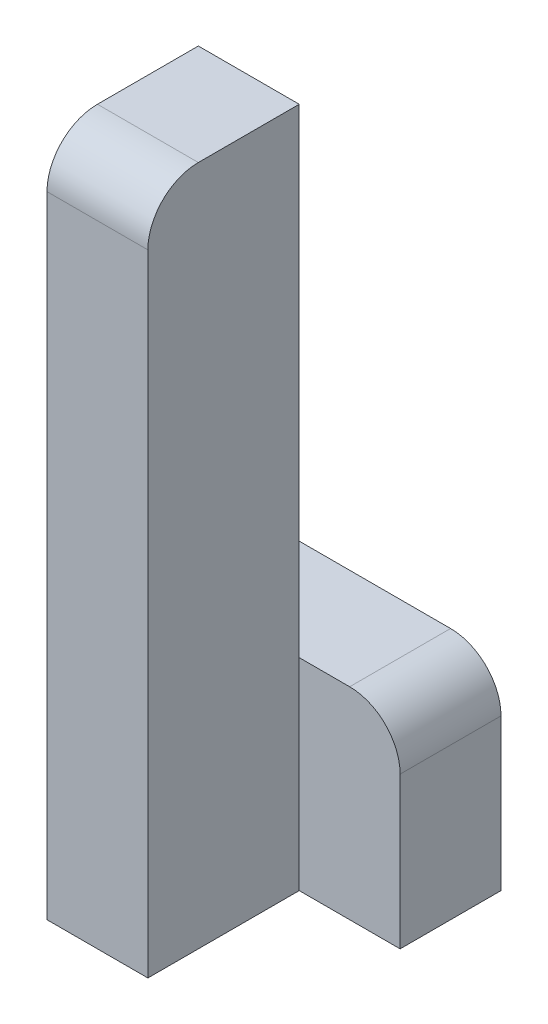
SolidWorks part; units mm, degrees
ref_plane "Front Plane" through (0, 0, 0) normal (0, 0, 1) x (1, 0, 0)
ref_plane "Top Plane" through (0, 0, 0) normal (0, 1, 0) x (1, 0, 0)
ref_plane "Right Plane" through (0, 0, 0) normal (1, 0, 0) x (0, 0, -1)
sketch "Sketch1" plane through (0, 0, 0) normal (0, 0, 1) x (1, 0, 0)
  line L1 (-30, -135) -> (-10, -135)
  line L2 (-10, -135) -> (-10, 0)
  line L3 (-10, 0) -> (-30, 0)
  line L4 (-30, 0) -> (-30, -135)
  dimension "D1" = 20
  dimension "Width" = 135
extrude "Boss-Extrude1" add sketch "Sketch1" along normal blind 30
sketch "Sketch2" plane through (0, 0, 0) normal (0, 0, 1) x (1, 0, 0)
  line L1 (-30, -135) -> (10, -135)
  line L2 (10, -135) -> (10, -95)
  line L3 (10, -95) -> (-30, -95)
  line L4 (-30, -95) -> (-30, -135)
  dimension "D1" = 40
  dimension "Width" = 40
extrude "Boss-Extrude2" add sketch "Sketch2" against normal blind 20
fillet "Fillet1" radius 10 2 edges at (10, -95, -10) (-20, 0, 30)
